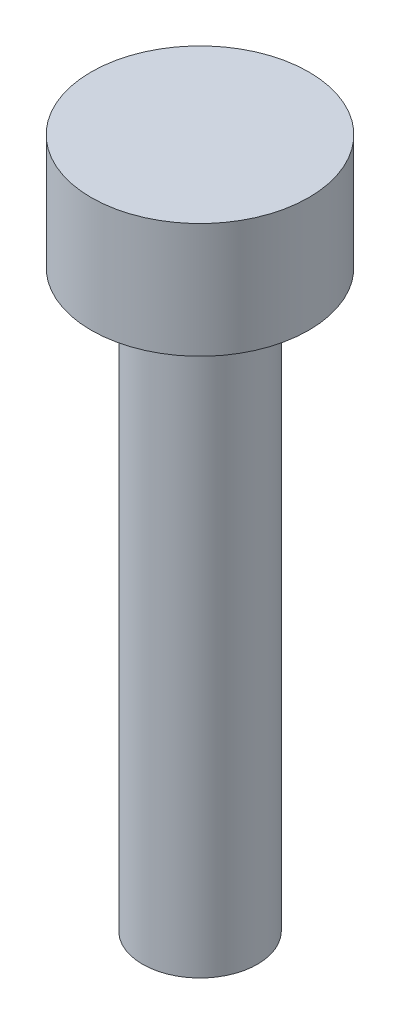
SolidWorks part; units mm, degrees
ref_plane "Alzado" through (0, 0, 0) normal (0, 0, 1) x (1, 0, 0)
ref_plane "Planta" through (0, 0, 0) normal (0, 1, 0) x (1, 0, 0)
ref_plane "Vista lateral" through (0, 0, 0) normal (1, 0, 0) x (0, 0, -1)
sketch "Croquis1" plane through (0, 0, 0) normal (0, 1, 0) x (1, 0, 0)
  circle A0 centre (0, 0) radius 1.5
  dimension "D1" = 3
extrude "Saliente-Extruir1" add sketch "Croquis1" along normal blind 15
sketch "Croquis2" plane through (0, 15, 0) normal (0, 1, 0) x (1, 0, 0)
  circle A0 centre (0, 0) radius 2.84
  dimension "D1" = 5.68
extrude "Saliente-Extruir2" add sketch "Croquis2" along normal blind 3
